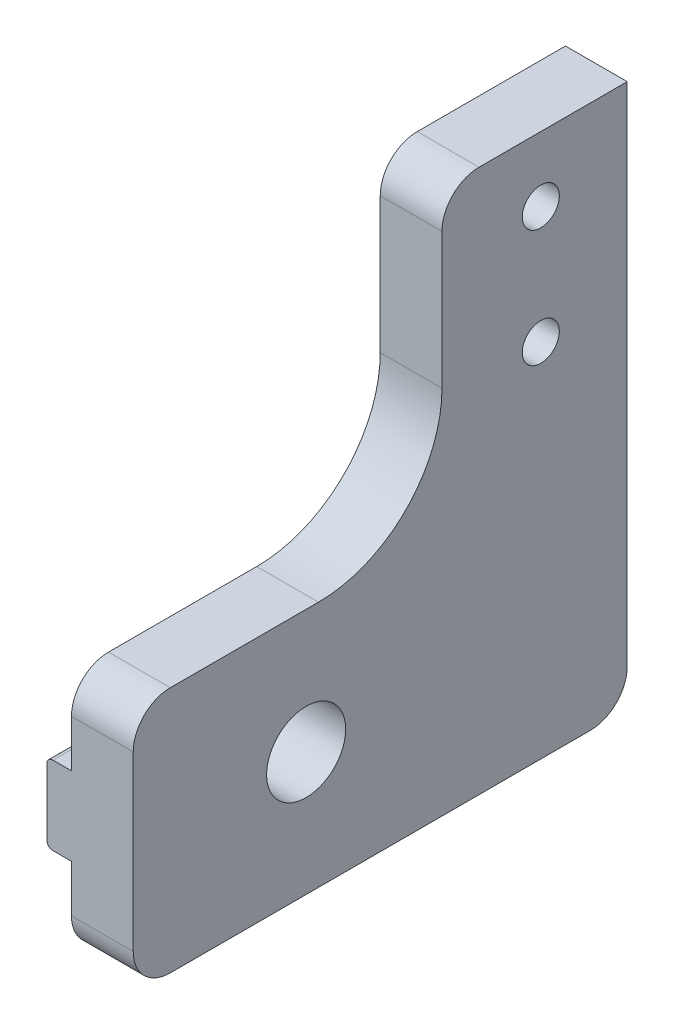
SolidWorks part; units mm, degrees
ref_plane "Front Plane" through (0, 0, 0) normal (0, 0, 1) x (1, 0, 0)
ref_plane "Top Plane" through (0, 0, 0) normal (0, 1, 0) x (1, 0, 0)
ref_plane "Right Plane" through (0, 0, 0) normal (1, 0, 0) x (0, 0, -1)
sketch "Sketch1" plane through (0, 0, 0) normal (1, 0, 0) x (0, 0, -1)
  line L0 (0, 0) -> (0, 20)
  line L5 (0, 20) -> (25, 20)
  line L6 (25, 20) -> (25, 44)
  line L7 (25, 44) -> (40, 44)
  line L8 (40, 44) -> (40, 0)
  line L9 (40, 0) -> (0, 0)
  line L10 (33, 38.75) -> (33, 29.25) construction
  circle A0 centre (33, 38.75) radius 1.5
  circle A1 centre (33, 29.25) radius 1.5
  point P11 (33, 34)
  point P13 (0, 10)
  dimension "D2" = 3
  dimension "D3" = 9.5
  dimension "D1" = 34
  dimension "D4" = 20
  dimension "D5" = 15
  dimension "D6" = 40
  dimension "D7" = 7
  dimension "D8" = 10
extrude "Boss-Extrude1" add sketch "Sketch1" along normal blind 5
sketch "Sketch3" plane through (0, 0, 0) normal (-1, 0, 0) x (0, 0, 1)
  line L0 (0, 20) -> (0, 0) construction
  line L1 (-40, 6.825) -> (0, 6.825)
  line L2 (-40, 6.825) -> (-40, 13.175)
  line L3 (-40, 13.175) -> (0, 13.175)
  line L4 (0, 6.825) -> (0, 13.175)
  line L5 (0, 20) -> (0, 0) construction
  line L6 (-40, 0) -> (-40, 44) construction
  point P6 (0, 10)
  dimension "D1" = 6.35
extrude "Boss-Extrude2" add sketch "Sketch3" along normal blind 2
fillet "Fillet1" radius 0.5 2 edges at (-2, 6.825, -20) (-2, 13.175, -20)
fillet "Fillet2" radius 3 4 edges at (2.5, 44, -25) (2.5, 20, 0) (2.5, 0, 0) (2.5, 0, -40)
sketch "Sketch4" plane through (5, 0, 0) normal (1, 0, 0) x (0, 0, -1)
  line L1 (0, 17) -> (0, 3) construction
  line L2 (0, 17) -> (0, 3) construction
  line L3 (25, 20) -> (3, 20) construction
  line L4 (25, 20) -> (3, 20) construction
  circle A0 centre (14, 10) radius 3.2004
  point P9 (0, 10)
  point P12 (14, 20)
  dimension "D1" = 6.4008
extrude "Cut-Extrude1" cut sketch "Sketch4" against normal through all
fillet "Fillet3" radius 10 1 edges at (2.5, 20, -25)
